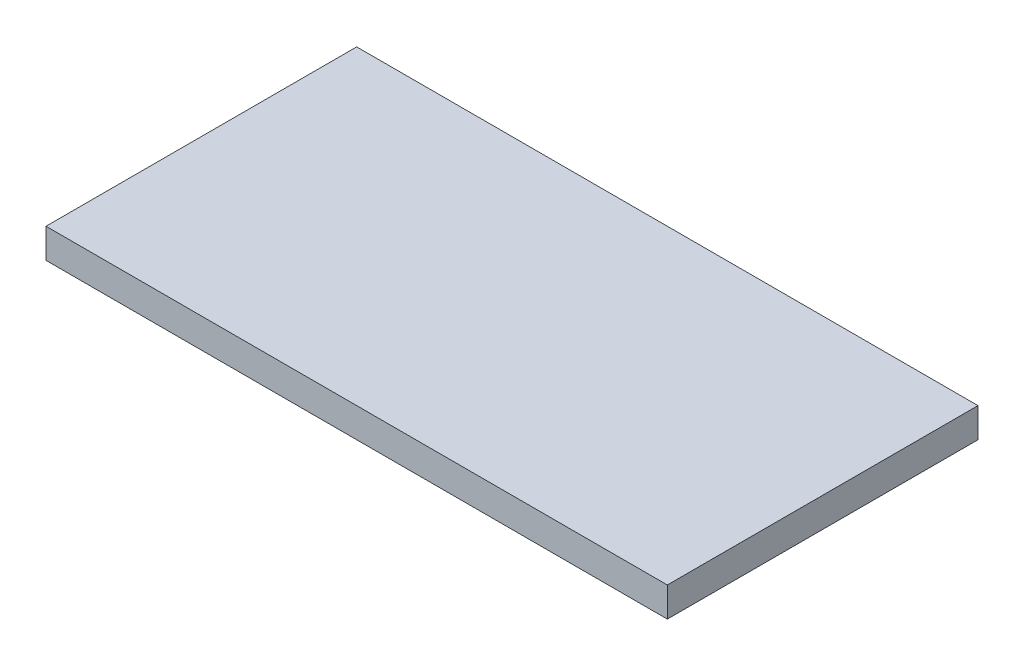
SolidWorks part; units mm, degrees
ref_plane "Front Plane" through (0, 0, 0) normal (0, 0, 1) x (1, 0, 0)
ref_plane "Top Plane" through (0, 0, 0) normal (0, 1, 0) x (1, 0, 0)
ref_plane "Right Plane" through (0, 0, 0) normal (1, 0, 0) x (0, 0, -1)
sketch "Sketch1" plane through (0, 0, 0) normal (0, 1, 0) x (1, 0, 0)
  line L1 (-42, 21) -> (42, 21)
  line L2 (-42, 21) -> (-42, -21)
  line L3 (-42, -21) -> (42, -21)
  line L4 (42, 21) -> (42, -21)
  line L5 (-42, 21) -> (42, -21) construction
  line L6 (-42, -21) -> (42, 21) construction
  point P0 (0, 0)
  dimension "D1" = 84
  dimension "D2" = 42
extrude "Boss-Extrude1" add sketch "Sketch1" along normal blind 4
